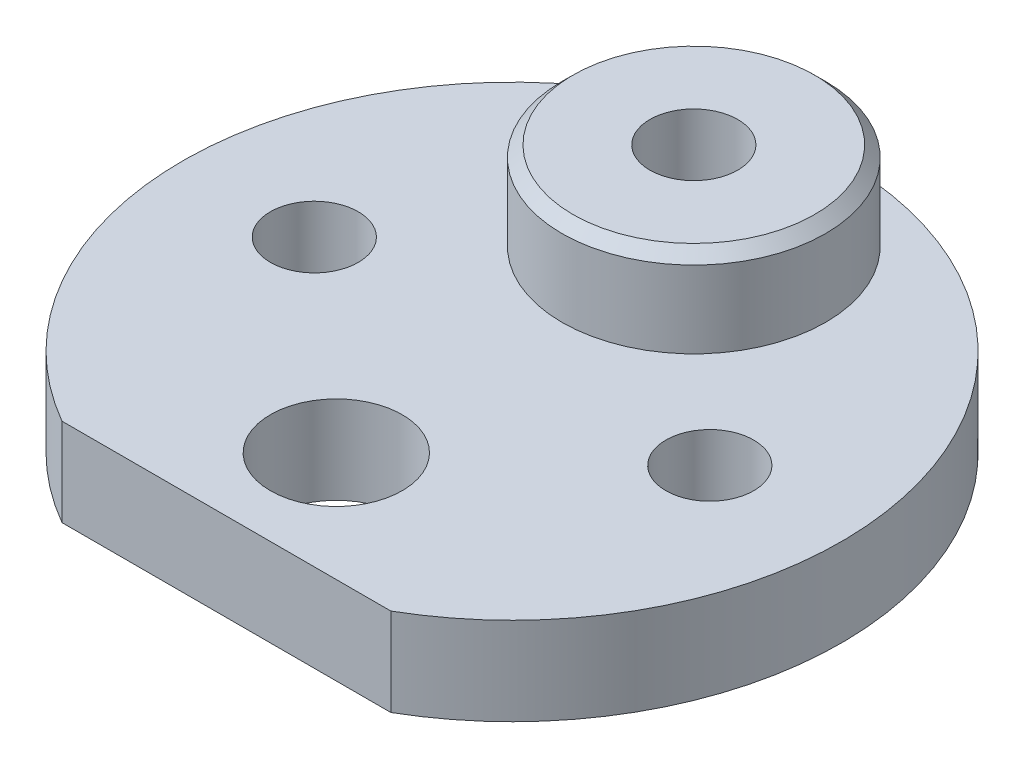
SolidWorks part; units mm, degrees
ref_plane "Front Plane" through (0, 0, 0) normal (0, 0, 1) x (1, 0, 0)
ref_plane "Top Plane" through (0, 0, 0) normal (0, 1, 0) x (1, 0, 0)
ref_plane "Right Plane" through (0, 0, 0) normal (1, 0, 0) x (0, 0, -1)
sketch "Sketch2" plane through (0, 0, 0) normal (0, 1, 0) x (1, 0, 0)
  line L0 (-24.6596, 0) -> (24.6635, 0) construction
  line L1 (-7.4833, -13) -> (7.4833, -13)
  arc A0 (7.4833, -13) -> (-7.4833, -13) centre (0, 0) ccw
  circle A1 centre (0, -8) radius 3
  circle A2 centre (-9, 0) radius 2
  circle A3 centre (9, 0) radius 2
  dimension "D1" = 30
  dimension "D2" = 4
  dimension "D3" = 4
  dimension "D4" = 6
  dimension "D5" = 9
  dimension "D6" = 9
  dimension "D7" = 8
  dimension "D8" = 13
extrude "Boss-Extrude1" add sketch "Sketch2" along normal blind 4
sketch "Sketch3" plane through (0, 4, 0) normal (0, 1, 0) x (1, 0, 0)
  circle A0 centre (0, 8.2729) radius 6
  dimension "D1" = 12
extrude "Boss-Extrude2" add sketch "Sketch3" along normal blind 4
sketch "Sketch4" plane through (0, 8, 0) normal (0, 1, 0) x (1, 0, 0)
  circle A0 centre (0, 8.2729) radius 2
  dimension "D1" = 4
extrude "Cut-Extrude1" cut sketch "Sketch4" against normal blind 15
chamfer "Chamfer1" distance 0.5 angle 45 1 edges at (0, 8, -2.2729)
